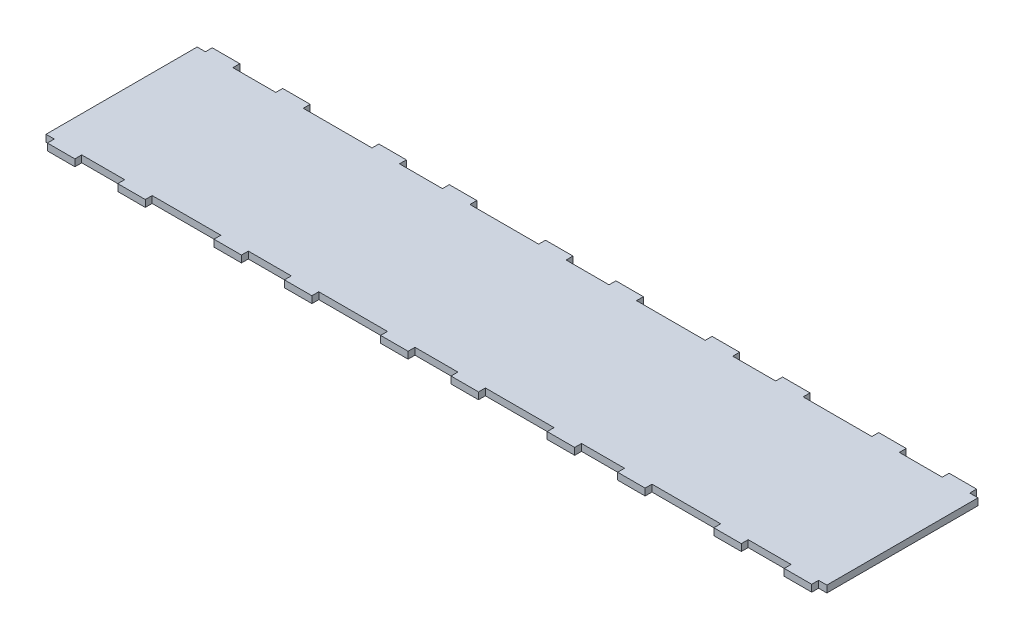
SolidWorks part; units mm, degrees
material "Cedar"
ref_plane "Front Plane" through (0, 0, 0) normal (0, 0, 1) x (1, 0, 0)
ref_plane "Top Plane" through (0, 0, 0) normal (0, 1, 0) x (1, 0, 0)
ref_plane "Right Plane" through (0, 0, 0) normal (1, 0, 0) x (0, 0, -1)
sketch "Sketch1" plane through (0, 0, 0) normal (0, 1, 0) x (1, 0, 0)
  line L1 (-360.8183, 76.2) -> (360.8183, 76.2)
  line L2 (-360.8183, 76.2) -> (-360.8183, -76.2)
  line L3 (-360.8183, -76.2) -> (360.8183, -76.2)
  line L4 (360.8183, 76.2) -> (360.8183, -76.2)
  line L5 (-360.8183, 76.2) -> (360.8183, -76.2) construction
  line L6 (-360.8183, -76.2) -> (360.8183, 76.2) construction
  point P0 (0, 0)
  dimension "D1" = 721.6366
  dimension "D2" = 152.4
extrude "Boss-Extrude1" add sketch "Sketch1" along normal blind 6.35
sketch "Sketch2" plane through (0, 6.35, 0) normal (0, 1, 0) x (1, 0, 0)
  line L0 (0, -76.2) -> (0, -69.85) construction
  line L1 (-32.5397, -69.85) -> (32.5397, -69.85) construction
  line L2 (-45.2397, -69.85) -> (-19.8397, -69.85) construction
  line L3 (-45.2397, -69.85) -> (-45.2397, -76.2) construction
  line L4 (-45.2397, -76.2) -> (-19.8397, -76.2) construction
  line L5 (-19.8397, -69.85) -> (-19.8397, -76.2)
  line L6 (-45.2397, -69.85) -> (-19.8397, -76.2) construction
  line L7 (-45.2397, -76.2) -> (-19.8397, -69.85) construction
  line L8 (-360.8183, -76.2) -> (360.8183, -76.2) construction
  line L9 (-19.8397, -69.85) -> (19.8397, -69.85)
  line L10 (19.8397, -69.85) -> (45.2397, -69.85) construction
  line L11 (19.8397, -69.85) -> (19.8397, -76.2)
  line L12 (19.8397, -76.2) -> (45.2397, -76.2) construction
  line L13 (45.2397, -69.85) -> (45.2397, -76.2) construction
  line L14 (19.8397, -69.85) -> (45.2397, -76.2) construction
  line L15 (19.8397, -76.2) -> (45.2397, -69.85) construction
  line L16 (19.8397, -76.2) -> (-19.8397, -76.2)
  line L17 (-45.2397, -76.2) -> (-45.2397, -69.85)
  line L18 (-45.2397, -69.85) -> (-76.9897, -69.85)
  line L19 (-76.9897, -69.85) -> (-76.9897, -76.2)
  line L20 (-76.9897, -76.2) -> (-45.2397, -76.2)
  line L21 (45.2397, -69.85) -> (76.9897, -69.85)
  line L22 (76.9897, -69.85) -> (76.9897, -76.2)
  line L23 (76.9897, -76.2) -> (45.2397, -76.2)
  line L24 (45.2397, -76.2) -> (45.2397, -69.85)
  point P5 (0, -69.85)
  point P6 (-32.5397, -73.025)
  point P11 (-32.5397, -69.85)
  point P17 (32.5397, -73.025)
  point P24 (32.5397, -69.85)
  dimension "D1" = 39.6793
  dimension "D2" = 25.4
  dimension "D3" = 6.35
  dimension "D4" = 76.9897
  dimension "D5" = 25.4
  dimension "D6" = 6.35
  dimension "D7" = 76.9897
extrude "Cut-Extrude1" cut sketch "Sketch2" against normal through all
pattern_linear "LPattern1" count 3 spacing 153.9793 along (1, 0, 0) count 3 spacing 153.9793 along (-1, 0, 0) of "Cut-Extrude1"
mirror "Mirror1" about plane through (0, 0, 0) normal (0, 0, 1) of "LPattern1", "Cut-Extrude1"
